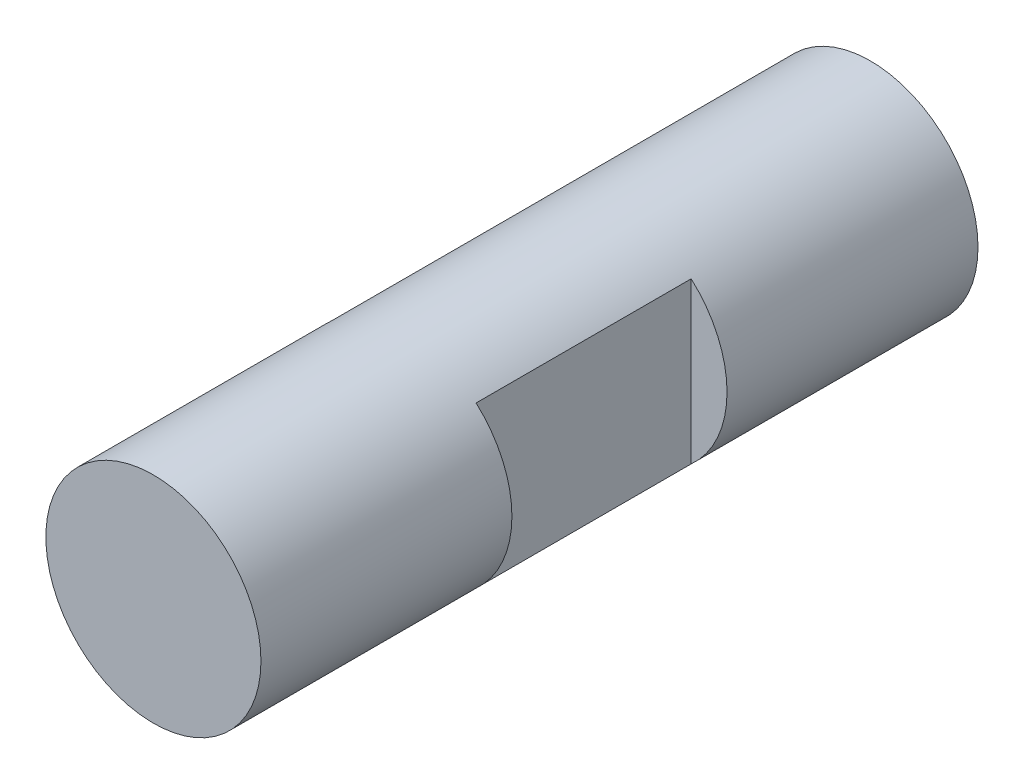
SolidWorks part; units mm, degrees
ref_plane "前视基准面" through (0, 0, 0) normal (0, 0, 1) x (1, 0, 0)
ref_plane "上视基准面" through (0, 0, 0) normal (0, 1, 0) x (1, 0, 0)
ref_plane "右视基准面" through (0, 0, 0) normal (1, 0, 0) x (0, 0, -1)
sketch "草图1" plane through (0, 0, 0) normal (0, 0, 1) x (1, 0, 0)
  circle A0 centre (0, 0) radius 6
  dimension "D1" = 12
extrude "凸台-拉伸1" add sketch "草图1" along normal blind 40
ref_plane "基准面2" through (4, 0, 0) normal (1, 0, 0) x (0, 0, -1)
sketch "草图3" plane through (4, 0, 0) normal (1, 0, 0) x (0, 0, -1)
  line L0 (0, -6) -> (0, 6) construction
  line L1 (-26, -4.5) -> (-14, -4.5)
  line L2 (-26, -4.5) -> (-26, 4.5)
  line L3 (-26, 4.5) -> (-14, 4.5)
  line L4 (-14, -4.5) -> (-14, 4.5)
  line L5 (-26, -4.5) -> (-14, 4.5) construction
  line L6 (-26, 4.5) -> (-14, -4.5) construction
  point P0 (-20, 0)
  dimension "D1" = 20
  dimension "D2" = 12
  dimension "D3" = 9
extrude "切除-拉伸1" cut sketch "草图3" along normal blind 40
mirror "镜向1" about plane through (0, 0, 0) normal (1, 0, 0) of "切除-拉伸1"
draft "拔模3" type of draft neutral plane draft angle 30 faces to draft 1 face at (-5, 0, 26) neutral plane through (-4, 0, 0) neutral plane normal (-1, 0, 0) parameters "D1"=30
